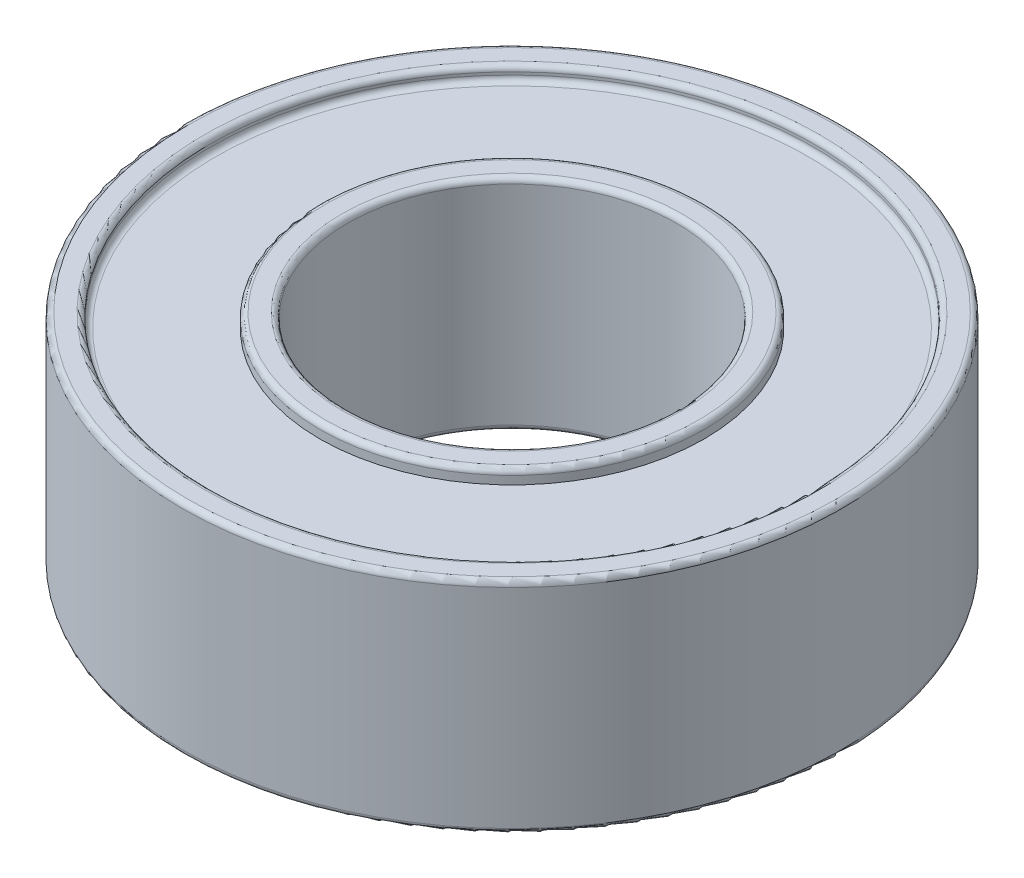
SolidWorks part; units mm, degrees
ref_plane "Front Plane" through (0, 0, 0) normal (0, 0, 1) x (1, 0, 0)
ref_plane "Top Plane" through (0, 0, 0) normal (0, 1, 0) x (1, 0, 0)
ref_plane "Right Plane" through (0, 0, 0) normal (1, 0, 0) x (0, 0, -1)
sketch "Sketch1" plane through (0, 0, 0) normal (0, 1, 0) x (1, 0, 0)
  circle A0 centre (0, 0) radius 6
  circle A1 centre (0, 0) radius 3
  dimension "D1" = 12
  dimension "D2" = 6
extrude "Boss-Extrude1" add sketch "Sketch1" along normal blind 4
sketch "Sketch2" plane through (0, 4, 0) normal (0, 1, 0) x (1, 0, 0)
  circle A0 centre (0, 0) radius 5.5
  circle A1 centre (0, 0) radius 3.5
  dimension "D1" = 7
  dimension "D2" = 11
extrude "Cut-Extrude1" cut sketch "Sketch2" against normal blind 0.25
ref_plane "Plane1" through (0, 2, 0) normal (0, 1, 0) x (1, 0, 0)
mirror "Mirror1" about plane through (0, 2, 0) normal (0, 1, 0) of "Cut-Extrude1"
fillet "Fillet1" radius 0.1 9 edges at (0, 4, 5.5) (0, 3.75, 5.5) (0, 0, 3) (0, 0, 3.5) (0, 4, 3.5) (0, 4, 3) (0, 0, 6) (0, 0.25, 5.5) (0, 4, 6)
